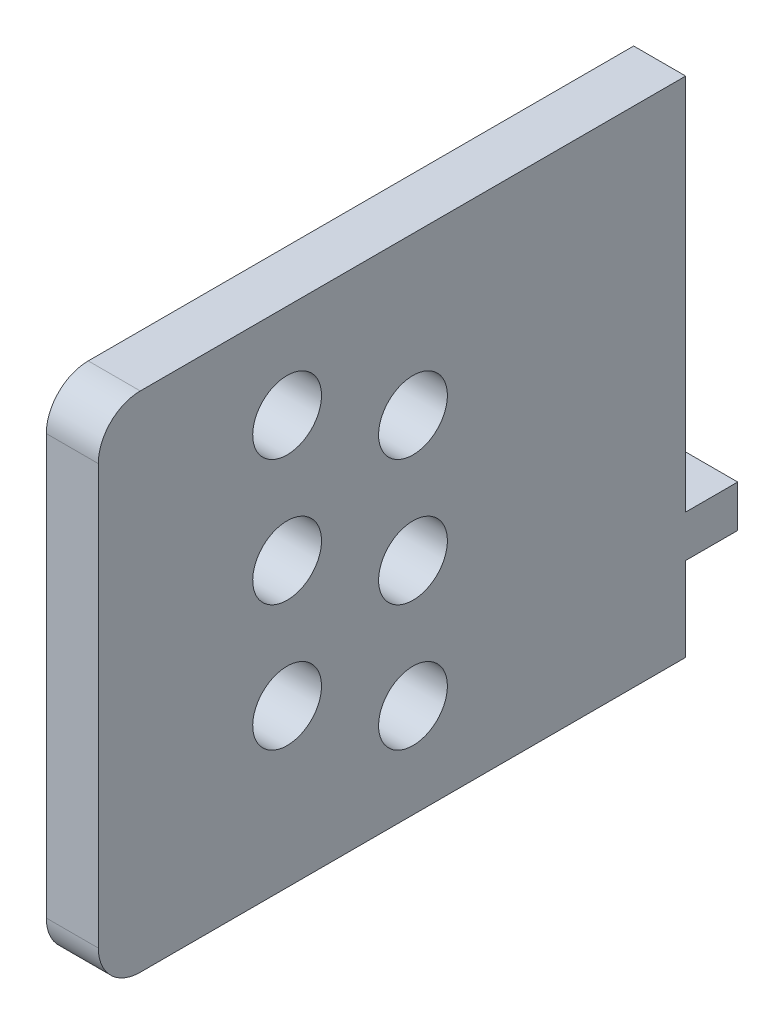
SolidWorks part; units mm, degrees
material "ASTM A36"
ref_plane "Front" through (0, 0, 0) normal (0, 0, 1) x (1, 0, 0)
ref_plane "Top" through (0, 0, 0) normal (0, 1, 0) x (1, 0, 0)
ref_plane "Side" through (0, 0, 0) normal (1, 0, 0) x (0, 0, -1)
sketch "Sketch1" plane through (0, 0, 0) normal (0, 0, 1) x (1, 0, 0)
  line L1 (0, 76.2) -> (7.874, 76.2)
  line L2 (0, 76.2) -> (0, 0)
  line L3 (0, 0) -> (7.874, 0)
  line L4 (7.874, 76.2) -> (7.874, 0)
  dimension "D1" = 76.2
  dimension "D2" = 7.874
extrude "Extrude1" add sketch "Sketch1" along normal blind 88.9
sketch "Sketch2" plane through (0, 0, 0) normal (-1, 0, 0) x (0, 0, 1)
  line L1 (88.9, 0) -> (88.9, 76.2) construction
  line L4 (88.9, 0) -> (0, 0) construction
  circle A0 centre (60.325, 23.8125) radius 5.207
  circle A1 centre (60.325, 42.8625) radius 5.207
  circle A2 centre (60.325, 61.9125) radius 5.207
  circle A3 centre (41.275, 33.3375) radius 5.207
  circle A4 centre (41.275, 52.3875) radius 5.207
  circle A5 centre (41.275, 14.2875) radius 5.207
  dimension "D1" = 10.414
  dimension "D3" = 28.575
  dimension "D4" = 19.05
  dimension "D2" = 14.2875
  dimension "D5" = 19.05
  dimension "D6" = 19.05
  dimension "D7" = 19.05
  dimension "D8" = 19.05
  dimension "D9" = 9.525
extrude "Cut-Extrude1" cut sketch "Sketch2" against normal through all
fillet "Fillet1" radius 6.35 2 edges at (3.937, 0, 88.9) (3.937, 76.2, 88.9)
sketch "Sketch3" plane through (0, 0, 0) normal (0, 0, 1) x (1, 0, 0)
  line L0 (7.874, 6.35) -> (7.874, 69.85) construction
  line L1 (0, 19.05) -> (7.874, 19.05)
  line L2 (0, 19.05) -> (0, 12.7)
  line L3 (0, 12.7) -> (7.874, 12.7)
  line L4 (7.874, 19.05) -> (7.874, 12.7)
  line L5 (7.874, 0) -> (0, 0) construction
  dimension "D1" = 6.35
  dimension "D2" = 12.7
extrude "Extrude2" add sketch "Sketch3" against normal blind 7.874
